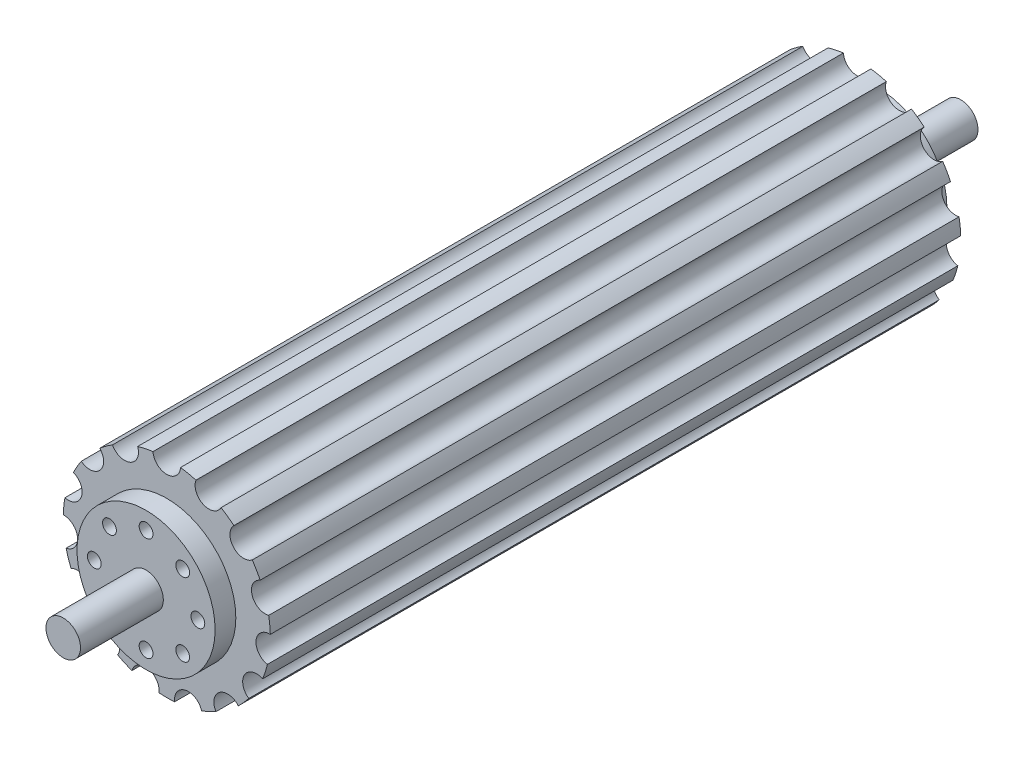
SolidWorks part; units mm, degrees
ref_plane "Front Plane" through (0, 0, 0) normal (0, 0, 1) x (1, 0, 0)
ref_plane "Top Plane" through (0, 0, 0) normal (0, 1, 0) x (1, 0, 0)
ref_plane "Right Plane" through (0, 0, 0) normal (1, 0, 0) x (0, 0, -1)
sketch "Sketch1" plane through (0, 0, 0) normal (0, 0, 1) x (1, 0, 0)
  circle A0 centre (0, 0) radius 15
  dimension "D1" = 30
extrude "Boss-Extrude1" add sketch "Sketch1" along normal blind 100
sketch "Sketch2" plane through (0, 0, 100) normal (0, 0, 1) x (1, 0, 0)
  circle A0 centre (0, 0) radius 2.5
  dimension "D1" = 5
extrude "Boss-Extrude3" add sketch "Sketch2" along normal blind 15 contours A0
sketch "Sketch4" plane through (0, 0, 100) normal (0, 0, 1) x (1, 0, 0)
  circle A0 centre (0, 0) radius 10
  circle A2 centre (0, 0) radius 2.5
  circle A3 centre (0, 0) radius 2.5
  dimension "D1" = 20
  dimension "D2" = 0
extrude "Boss-Extrude4" add sketch "Sketch4" along normal blind 3
ref_plane "Plane1" through (0, 0, 50) normal (0, 0, 1) x (1, 0, 0)
mirror "Mirror1" about plane through (0, 0, 50) normal (0, 0, 1) of "Boss-Extrude4", "Boss-Extrude3"
sketch "Sketch7" plane through (0, 0, 103) normal (0, 0, 1) x (1, 0, 0)
  circle A0 centre (0, 0) radius 7.5 construction
  circle A1 centre (0, 7.5) radius 1
  circle A2 centre (5.3033, 5.3033) radius 1
  circle A3 centre (7.5, 0) radius 1
  circle A4 centre (5.3033, -5.3033) radius 1
  circle A5 centre (0, -7.5) radius 1
  circle A6 centre (-5.3033, -5.3033) radius 1
  circle A7 centre (-7.5, 0) radius 1
  circle A8 centre (-5.3033, 5.3033) radius 1
  point P22 (0, 0)
  dimension "D1" = 15
  dimension "D2" = 2
  dimension "D3" = 8
extrude "Cut-Extrude1" cut sketch "Sketch7" against normal blind 3
sketch "Sketch8" plane through (0, 0, 100) normal (0, 0, 1) x (1, 0, 0)
  circle A0 centre (0, 15) radius 2
  circle A1 centre (0, 0) radius 15 construction
  circle A2 centre (6.101, 13.7032) radius 2
  circle A3 centre (11.1472, 10.037) radius 2
  circle A4 centre (14.2658, 4.6353) radius 2
  circle A5 centre (14.9178, -1.5679) radius 2
  circle A6 centre (12.9904, -7.5) radius 2
  circle A7 centre (8.8168, -12.1353) radius 2
  circle A8 centre (3.1187, -14.6722) radius 2
  circle A9 centre (-3.1187, -14.6722) radius 2
  circle A10 centre (-8.8168, -12.1353) radius 2
  circle A11 centre (-12.9904, -7.5) radius 2
  circle A12 centre (-14.9178, -1.5679) radius 2
  circle A13 centre (-14.2658, 4.6353) radius 2
  circle A14 centre (-11.1472, 10.037) radius 2
  circle A15 centre (-6.101, 13.7032) radius 2
  point P35 (0, 0)
  dimension "D1" = 4
  dimension "D2" = 15
extrude "Cut-Extrude2" cut sketch "Sketch8" against normal through all
